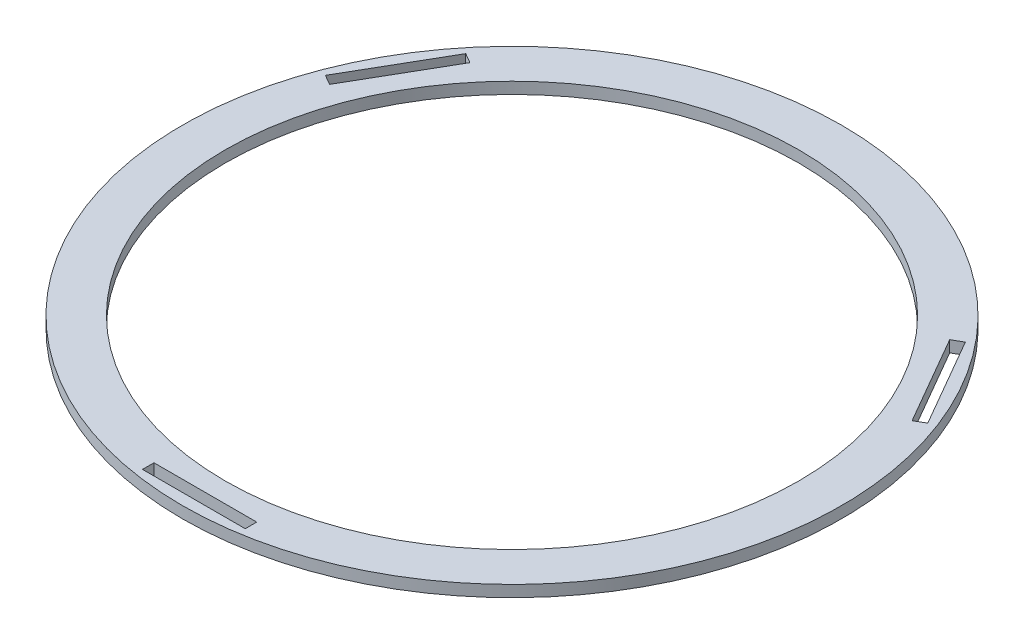
SolidWorks part; units mm, degrees
ref_plane "Front Plane" through (0, 0, 0) normal (0, 0, 1) x (1, 0, 0)
ref_plane "Top Plane" through (0, 0, 0) normal (0, 1, 0) x (1, 0, 0)
ref_plane "Right Plane" through (0, 0, 0) normal (1, 0, 0) x (0, 0, -1)
sketch "Sketch1" plane through (0, 0, 0) normal (0, 1, 0) x (1, 0, 0)
  circle A0 centre (0, 0) radius 250
  circle A1 centre (0, 0) radius 287.2635
  circle A2 centre (0, 0) radius 250 construction
  arc A4 (75, -277.3) -> (277.6488, 73.6981) centre (0, 0) ccw construction
extrude "Boss-Extrude1" add sketch "Sketch1" along normal blind 10
sketch "Sketch2" plane through (0, 10, 0) normal (0, 1, 0) x (1, 0, 0)
  line L0 (-44.7794, -277.3) -> (44.7794, -277.3)
  line L1 (44.7794, -277.3) -> (44.7794, -267.3)
  line L2 (44.7794, -267.3) -> (-44.7794, -267.3)
  line L3 (-44.7794, -267.3) -> (-44.7794, -277.3)
extrude "Cut-Extrude1" cut sketch "Sketch2" against normal blind 10
pattern_circular "CirPattern1" count 3 over 360 about axis through (0, 0, 0) along (0, 1, 0) of "Cut-Extrude1"
